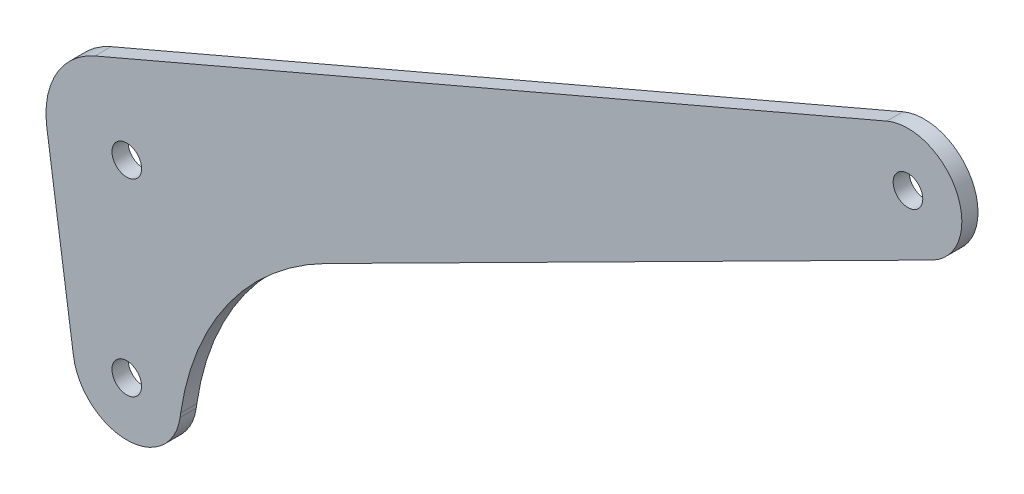
SolidWorks part; units mm, degrees
ref_plane "Plan de face" through (0, 0, 0) normal (0, 0, 1) x (1, 0, 0)
ref_plane "Plan de dessus" through (0, 0, 0) normal (0, 1, 0) x (1, 0, 0)
ref_plane "Plan de droite" through (0, 0, 0) normal (1, 0, 0) x (0, 0, -1)
sketch "Esquisse1" plane through (0, 0, 0) normal (0, 0, 1) x (1, 0, 0)
  line L0 (0, 0) -> (0, 35)
  line L1 (0, 35) -> (145.0092, 102.6189)
  dimension "D1" = 35
  dimension "D2" = 115
  dimension "D3" = 160
sketch "Esquisse4" plane through (0, 0, 0) normal (0, 0, 1) x (1, 0, 0)
  line L0 (149.5166, 93.6923) -> (6.761, 21.6101)
  line L1 (141.0683, 111.8096) -> (-5.9113, 48.7861)
  line L2 (-9.8974, -1.4286) -> (-14.8461, 32.8571)
  line L3 (14.8461, 32.8571) -> (9.8974, -1.4286)
  circle A0 centre (0, 0) radius 10
  circle A1 centre (0, 35) radius 15
  circle A2 centre (145.0092, 102.6189) radius 10
  arc A3 (10.0127, -0.6298) -> (36.9632, 36.8602) centre (59.4999, -7.7727) cw
  dimension "D1" = 30
  dimension "D2" = 20
  dimension "D3" = 20
  dimension "D4" = 50
extrude "Boss.-Extru.1" add sketch "Esquisse4" along normal blind 3 contours A2 | A2 L1 A1 L3 L0 | A1 | A1 L2 A0 L3 L0 | A0 | L3 A3 L0 | A1 L0 L3
sketch "Esquisse6" plane through (0, 0, 3) normal (0, 0, 1) x (1, 0, 0)
  circle A0 centre (145.0092, 102.6189) radius 3
  circle A1 centre (0, 35) radius 3
  circle A2 centre (0, 0) radius 3
  dimension "D1" = 6
extrude "Enlèv. mat.-Extru.1" [suppressed] cut sketch "Esquisse6" against normal through all
sketch "Esquisse7" [suppressed] plane through (0, 0, 0) normal (0, 0, 1) x (1, 0, 0)
  line L1 (185, -10) -> (-15, -10)
  line L2 (185, -10) -> (185, 190)
  line L3 (185, 190) -> (-15, 190)
  line L4 (-15, -10) -> (-15, 190)
  line L5 (185, -10) -> (-15, 190) construction
  line L6 (185, 190) -> (-15, -10) construction
  arc A0 (-6.1261, 48.692) -> (-14.8461, 32.8571) centre (0, 35) ccw construction
  arc A1 (-9.8974, -1.4286) -> (9.8974, -1.4286) centre (0, 0) ccw construction
  point P0 (85, 90)
  dimension "D1" = 200
  dimension "D2" = 200
fillet "Congé1" [suppressed] radius 3
hole_wizard "Dégagement M51" positions "Esquisse8" profile "Esquisse9" hole size "M5" standard "ISO" end condition through all
sketch "Esquisse8" plane through (0, 0, 3) normal (0, 0, -1) x (-1, 0, 0)
  point P0 (-145.0092, 102.6189)
  point P3 (0, 35)
  point P6 (0, 0)
sketch "Esquisse9" plane through (145.0092, 102.6189, 3) normal (1, 0, 0) x (0, -1, 0)
  line L0 (0, 0) -> (0, 3)
  line L1 (0, 3) -> (2.75, 3)
  line L2 (2.75, 3) -> (2.75, 0)
  line L5 (2.75, 0) -> (0, 0)
  line L11 (0, -6.35) -> (0, 107.95) construction
  dimension "Diamètre du perçage jusqu'au prochain" = 5.5
  dimension "Profondeur du perçage jusqu'au prochain" = 3
sketch "Esquisse10" plane through (0, 0, 0) normal (0, 0, -1) x (-1, 0, 0)
  line L1 (241.3036, -166.3306) -> (-241.3036, -166.3306)
  line L2 (241.3036, -166.3306) -> (241.3036, 166.3306)
  line L3 (241.3036, 166.3306) -> (-241.3036, 166.3306)
  line L4 (-241.3036, -166.3306) -> (-241.3036, 166.3306)
  line L5 (241.3036, -166.3306) -> (-241.3036, 166.3306) construction
  line L6 (241.3036, 166.3306) -> (-241.3036, -166.3306) construction
  point P0 (0, 0)
extrude "Enlèv. mat.-Extru.2" [suppressed] cut sketch "Esquisse10" against normal blind 14
fillet "Congé2" [suppressed] radius 3
